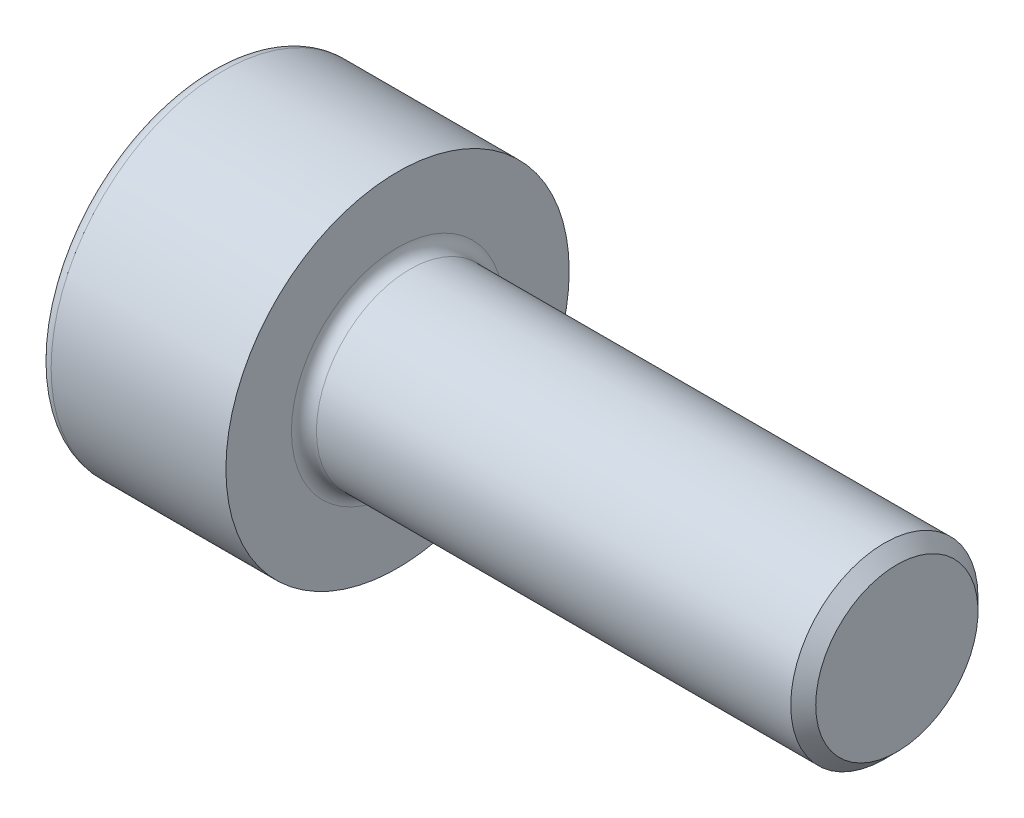
SolidWorks part; units mm, degrees
ref_plane "Front" through (0, 0, 0) normal (0, 0, 1) x (1, 0, 0)
ref_plane "Top" through (0, 0, 0) normal (0, 1, 0) x (1, 0, 0)
ref_plane "Right" through (0, 0, 0) normal (1, 0, 0) x (0, 0, -1)
sketch "Esquisse1" plane through (0, 0, 0) normal (0, 0, 1) x (1, 0, 0)
  line L0 (0, 0) -> (11, 0) construction
  line L1 (0, 0) -> (0, 2.75)
  line L2 (0, 2.75) -> (3, 2.75)
  line L3 (3, 2.75) -> (3, 1.5)
  line L4 (3, 1.5) -> (11, 1.5)
  line L5 (11, 1.5) -> (11, 0)
  line L6 (0, 0) -> (11, 0)
  dimension "D1" = 3
  dimension "D2" = 8
  dimension "D3" = 3
  dimension "D4" = 5.5
revolve "Révolution1" add sketch "Esquisse1" angle 360 about L0
chamfer "Chanfrein1" distance 0.2 angle 45 1 edges at (11, 0, 1.5)
fillet "Congé1" radius 0.2 2 edges at (3, 0, 1.5) (0, 0, 2.75)
sketch "Esquisse2" plane through (0, 0, 0) normal (-1, 0, 0) x (0, 0, 1)
  line L1 (0.739, -1.28) -> (1.478, 0)
  line L2 (1.478, 0) -> (0.739, 1.28)
  line L3 (0.739, 1.28) -> (-0.739, 1.28)
  line L4 (-0.739, 1.28) -> (-1.478, 0)
  line L5 (-1.478, 0) -> (-0.739, -1.28)
  line L6 (-0.739, -1.28) -> (0.739, -1.28)
  circle A0 centre (0, 0) radius 1.28 construction
  dimension "D1" = 2.56
extrude "Enlèv. mat.-Extru.1" cut sketch "Esquisse2" against normal blind 1.3
